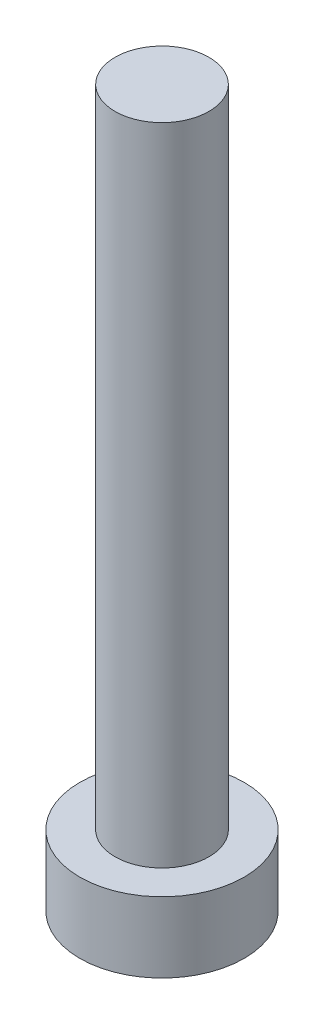
SolidWorks part; units mm, degrees
material "Plain Carbon Steel"
ref_plane "Front Plane" through (0, 0, 0) normal (0, 0, 1) x (1, 0, 0)
ref_plane "Top Plane" through (0, 0, 0) normal (0, 1, 0) x (1, 0, 0)
ref_plane "Right Plane" through (0, 0, 0) normal (1, 0, 0) x (0, 0, -1)
sketch "Sketch1" plane through (0, 0, 0) normal (0, 1, 0) x (1, 0, 0)
  circle A0 centre (0, 0) radius 7
  dimension "D1" = 14
extrude "Boss-Extrude1" add sketch "Sketch1" along normal blind 6
sketch "Sketch2" plane through (0, 6, 0) normal (0, 1, 0) x (1, 0, 0)
  circle A0 centre (0, 0) radius 4
  dimension "D1" = 8
extrude "Boss-Extrude2" add sketch "Sketch2" along normal blind 55
